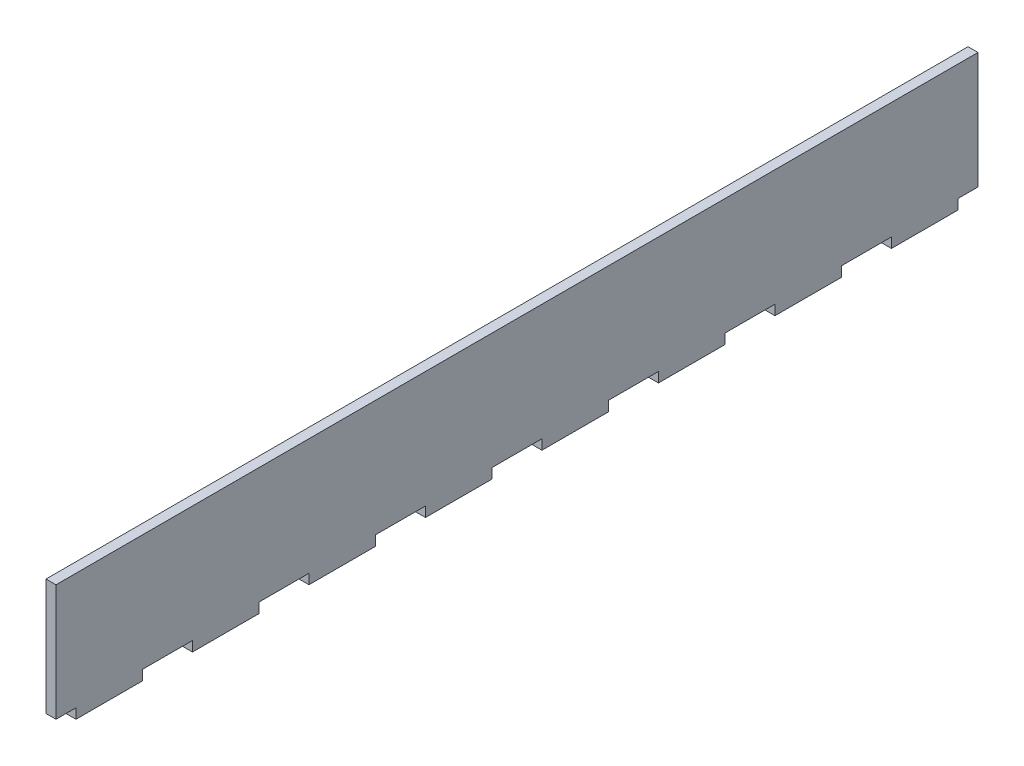
SolidWorks part; units mm, degrees
ref_plane "Front Plane" through (0, 0, 0) normal (0, 0, 1) x (1, 0, 0)
ref_plane "Top Plane" through (0, 0, 0) normal (0, 1, 0) x (1, 0, 0)
ref_plane "Right Plane" through (0, 0, 0) normal (1, 0, 0) x (0, 0, -1)
sketch "Sketch1" plane through (0, 0, 0) normal (1, 0, 0) x (0, 0, -1)
  line L0 (26, 0) -> (41, 0)
  line L1 (0, 0) -> (6, 0)
  line L2 (0, 0) -> (0, 35)
  line L3 (0, 35) -> (277, 35)
  line L4 (277, 0) -> (277, 35)
  line L7 (41, 0) -> (41, -3)
  line L8 (6, 0) -> (6, -3)
  line L9 (6, -3) -> (26, -3)
  line L10 (26, 0) -> (26, -3)
  line L13 (41, -3) -> (61, -3)
  line L14 (61, 0) -> (61, -3)
  line L15 (76, 0) -> (76, -3)
  line L16 (76, -3) -> (96, -3)
  line L17 (96, 0) -> (96, -3)
  line L18 (111, 0) -> (111, -3)
  line L19 (111, -3) -> (131, -3)
  line L20 (131, 0) -> (131, -3)
  line L21 (146, 0) -> (146, -3)
  line L22 (146, -3) -> (166, -3)
  line L23 (166, 0) -> (166, -3)
  line L24 (181, 0) -> (181, -3)
  line L25 (181, -3) -> (201, -3)
  line L26 (201, 0) -> (201, -3)
  line L27 (216, 0) -> (216, -3)
  line L28 (216, -3) -> (236, -3)
  line L29 (236, 0) -> (236, -3)
  line L30 (251, 0) -> (251, -3)
  line L31 (251, -3) -> (271, -3)
  line L32 (271, 0) -> (271, -3)
  line L33 (61, 0) -> (76, 0)
  line L34 (96, 0) -> (111, 0)
  line L35 (131, 0) -> (146, 0)
  line L36 (166, 0) -> (181, 0)
  line L37 (201, 0) -> (216, 0)
  line L38 (236, 0) -> (251, 0)
  line L39 (271, 0) -> (277, 0)
  dimension "D1" = 20
  dimension "D2" = 6
  dimension "D3" = 277
  dimension "D4" = 3
  dimension "D6" = 35
  dimension "D7" = 15
  dimension "D5" = 8
extrude "Boss-Extrude1" add sketch "Sketch1" along normal blind 3 contours L3 L4 L39 L32 L31 L30 L38 L29 L28 L27 L37 L26 L25 L24 L36 L23 L22 L21 L35 L20 L19 L18 L34 L17 L16 L15 L33 L14 L13 L7 L0 L10 L9 L8 L1 L2
